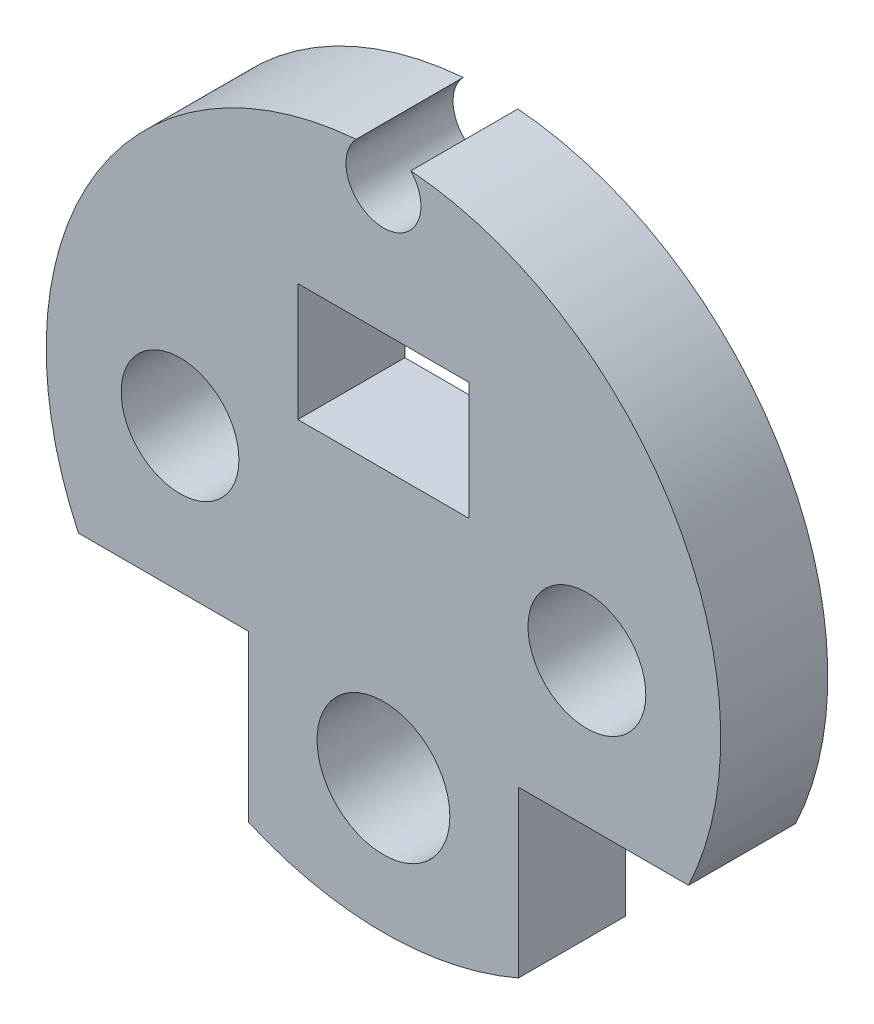
SolidWorks part; units mm, degrees
ref_plane "Plan de face" through (0, 0, 0) normal (0, 0, 1) x (1, 0, 0)
ref_plane "Plan de dessus" through (0, 0, 0) normal (0, 1, 0) x (1, 0, 0)
ref_plane "Plan de droite" through (0, 0, 0) normal (1, 0, 0) x (0, 0, -1)
sketch "Esquisse1" plane through (0, 0, 0) normal (0, 0, 1) x (1, 0, 0)
  circle A0 centre (0, 0) radius 15.75
extrude "Boss.-Extru.1" add sketch "Esquisse1" along normal blind 5
sketch "Esquisse2" plane through (0, 0, 0) normal (0, 0, -1) x (-1, 0, 0)
  line L0 (0, -13.5149) -> (0, 0) construction
  line L1 (-2.75, -13.5149) -> (2.75, -13.5149)
  line L2 (-2.75, -13.5149) -> (-2.75, -16.5)
  line L3 (-2.75, -16.5) -> (2.75, -16.5)
  line L4 (2.75, -13.5149) -> (2.75, -16.5)
  dimension "D1" = 5.5
  dimension "D2" = 16.5
extrude "Boss.-Extru.2" add sketch "Esquisse2" against normal offset from surface (2.7 mm away) 2.3 up to face at (15.75, 0, 5)
sketch "Esquisse3" plane through (0, 0, 5) normal (0, 0, 1) x (1, 0, 0)
  circle A0 centre (0, 14.5) radius 1.75
  circle A1 centre (9.5, 0) radius 2.75
  circle A2 centre (-9.5, 0) radius 2.75
  circle A3 centre (0, -9.5) radius 3.1
  circle A4 centre (0, -9.5) radius 3.1 construction
  dimension "D1" = 3.5
  dimension "D2" = 5.5
extrude "Enlèv. mat.-Extru.1" cut sketch "Esquisse3" against normal through all
sketch "Esquisse4" plane through (0, 0, 5) normal (0, 0, 1) x (1, 0, 0)
  line L1 (-14.2467, -6.7153) -> (-6.3042, -6.7153)
  line L2 (-14.2467, -6.7153) -> (-14.2467, -14.4333)
  line L3 (-14.2467, -14.4333) -> (-6.3042, -14.4333)
  line L4 (-6.3042, -6.7153) -> (-6.3042, -14.4333)
  arc A0 (-1.2754, 15.6983) -> (1.2754, 15.6983) centre (0, 0) ccw construction
extrude "Enlèv. mat.-Extru.2" cut sketch "Esquisse4" against normal through all
mirror "Symétrie1" about plane through (0, 0, 0) normal (1, 0, 0) of "Enlèv. mat.-Extru.2"
sketch "Esquisse5" plane through (0, 0, 5) normal (0, 0, 1) x (1, 0, 0)
  line L0 (0, 3) -> (0, 0) construction
  line L1 (-4, 8.5) -> (4, 8.5)
  line L2 (-4, 8.5) -> (-4, 3)
  line L3 (-4, 3) -> (4, 3)
  line L4 (4, 8.5) -> (4, 3)
  dimension "D1" = 8
  dimension "D2" = 5.5
  dimension "D3" = 3
extrude "Enlèv. mat.-Extru.3" cut sketch "Esquisse5" against normal through all
